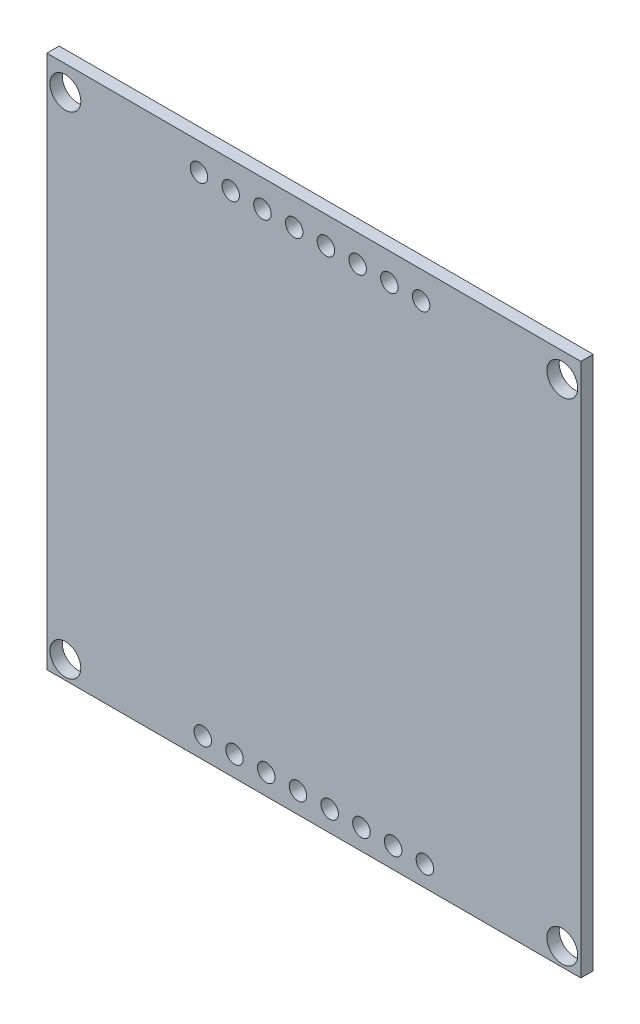
SolidWorks part; units mm, degrees
material "ABS"
ref_plane "Plano frontal" through (0, 0, 0) normal (0, 0, 1) x (1, 0, 0)
ref_plane "Plano superior" through (0, 0, 0) normal (0, 1, 0) x (1, 0, 0)
ref_plane "Plano direito" through (0, 0, 0) normal (1, 0, 0) x (0, 0, -1)
sketch "Esboço1" plane through (0, 0, 0) normal (0, 0, 1) x (1, 0, 0)
  line L0 (177.8616, 484.862) -> (801.195, 484.862) construction
  line L1 (0, 0) -> (43.25, 0)
  line L2 (0, 0) -> (0, 43.25)
  line L3 (0, 43.25) -> (43.25, 43.25)
  line L4 (43.25, 0) -> (43.25, 43.25)
  line L5 (98.8333, 296.5) -> (494.1667, 296.5) construction
  line L6 (21.625, 43.25) -> (21.625, 0) construction
  line L7 (0, 21.3634) -> (43.25, 21.3634) construction
  circle A0 centre (1.5, 41.25) radius 1.25
  circle A1 centre (12.3226, 41.05) radius 0.7074
  circle A2 centre (41.75, 41.25) radius 1.25
  circle A3 centre (14.8926, 41.0474) radius 0.7074
  circle A4 centre (17.4626, 41.0447) radius 0.7074
  circle A5 centre (20.0326, 41.0421) radius 0.7074
  circle A6 centre (22.6026, 41.0394) radius 0.7074
  circle A7 centre (25.1726, 41.0368) radius 0.7074
  circle A8 centre (27.7426, 41.0341) radius 0.7074
  circle A9 centre (30.3126, 41.0315) radius 0.7074
  circle A10 centre (30.62, 1.6767) radius 0.7074
  circle A11 centre (28.05, 1.6767) radius 0.7074
  circle A12 centre (25.48, 1.6767) radius 0.7074
  circle A13 centre (22.91, 1.6767) radius 0.7074
  circle A14 centre (20.34, 1.6767) radius 0.7074
  circle A15 centre (17.77, 1.6767) radius 0.7074
  circle A16 centre (15.2, 1.6767) radius 0.7074
  circle A17 centre (41.75, 1.4767) radius 1.25
  circle A18 centre (12.63, 1.6767) radius 0.7074
  circle A19 centre (1.5, 1.4767) radius 1.25
  dimension "D3" = 2.5
  dimension "D1" = 43.25
  dimension "D2" = 43.25
  dimension "D4" = 1.5
  dimension "D5" = 2
  dimension "D7" = 2.57
  dimension "D8" = 2.2
  dimension "D9" = 8
  dimension "D10" = 2.57
  dimension "D6" = 8
extrude "Ressalto-extrusão2" add sketch "Esboço1" along normal blind 1
